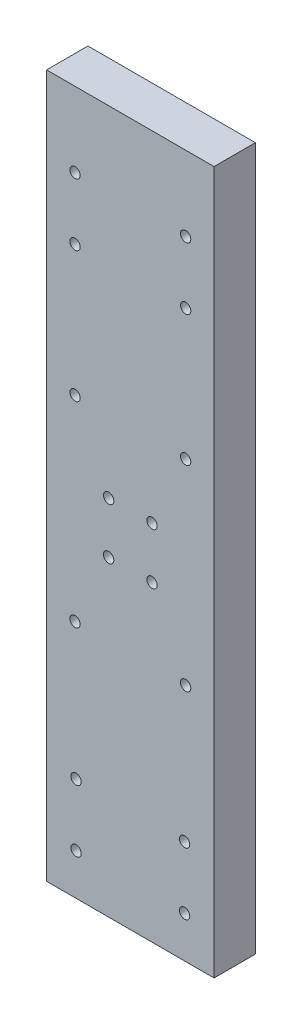
SolidWorks part; units mm, degrees
ref_plane "Front Plane" through (0, 0, 0) normal (0, 0, 1) x (1, 0, 0)
ref_plane "Top Plane" through (0, 0, 0) normal (0, 1, 0) x (1, 0, 0)
ref_plane "Right Plane" through (0, 0, 0) normal (1, 0, 0) x (0, 0, -1)
sketch "Sketch1" plane through (0, 0, 0) normal (0, 0, 1) x (1, 0, 0)
  line L0 (0, 44.76) -> (16.2, 44.76) construction
  line L1 (0, 12.5) -> (16.2, 12.5) construction
  line L2 (0, 20.5) -> (16.2, 20.5) construction
  line L4 (0, 0) -> (0, 67.99)
  line L5 (0, 0) -> (16.2, 0)
  line L6 (0, 67.99) -> (16.2, 67.99)
  line L7 (16.2, 67.99) -> (16.2, 0)
  line L8 (0, 52.76) -> (16.2, 52.76) construction
  circle A16 centre (6, 30.15) radius 0.5
  circle A17 centre (10.2, 30.15) radius 0.5
  circle A18 centre (10.2, 35.11) radius 0.5
  circle A19 centre (13.45, 60.76) radius 0.5
  circle A20 centre (13.45, 54.76) radius 0.5
  circle A21 centre (2.75, 60.76) radius 0.5
  circle A22 centre (6, 35.11) radius 0.5
  circle A23 centre (2.75, 42.11) radius 0.5
  circle A24 centre (2.85, 10) radius 0.5
  circle A25 centre (13.35, 10) radius 0.5
  circle A26 centre (13.35, 4) radius 0.5
  circle A27 centre (2.85, 4) radius 0.5
  circle A28 centre (13.45, 42.11) radius 0.5
  circle A29 centre (2.75, 54.76) radius 0.5
  circle A30 centre (13.45, 23.15) radius 0.5
  circle A31 centre (2.75, 23.15) radius 0.5
  dimension "D1" = 2.85
  dimension "D2" = 2.85
  dimension "D3" = 16.2
  dimension "D4" = 4
  dimension "D5" = 4
  dimension "D6" = 6
  dimension "D7" = 6
  dimension "D8" = 2.85
  dimension "D9" = 2.85
  dimension "D10" = 2.5
  dimension "D11" = 8
  dimension "D12" = 24.26
  dimension "D13" = 8
  dimension "D14" = 2.75
  dimension "D15" = 6
  dimension "D16" = 2.65
  dimension "D17" = 9.65
  dimension "D18" = 2.75
  dimension "D19" = 6
  dimension "D20" = 2.65
  dimension "D21" = 9.65
  dimension "D22" = 2.75
  dimension "D23" = 2.75
  dimension "D24" = 6
  dimension "D25" = 6
  dimension "D26" = 2.65
  dimension "D27" = 9.65
  dimension "D28" = 9.65
  dimension "D29" = 2.65
  dimension "D30" = 15.23
  dimension "D31" = 2.75
  dimension "D32" = 2.75
  dimension "D33" = 2
  dimension "D34" = 8
  dimension "D39" = 2.75
  dimension "D40" = 2.75
  dimension "D41" = 2
  dimension "D42" = 8
extrude "Boss-Extrude1" add sketch "Sketch1" along normal blind 4
equation "\"D12@Sketch1\"= \"HL@parametersSketch@prostheticParameters.SLDPRT\" * 0.196 - 4 - 8'Thumb PIP Length"
equation "\"D30@Sketch1\"= \"HL@parametersSketch@prostheticParameters.SLDPRT\" * 0.158 - 4 - 10 'Thumb DIP Length - Fingertip"
equation "\"D3@Sketch1\"= \"fingerWidth@parametersSketch@prostheticParameters.SLDPRT\"'Thumb Breadth"
